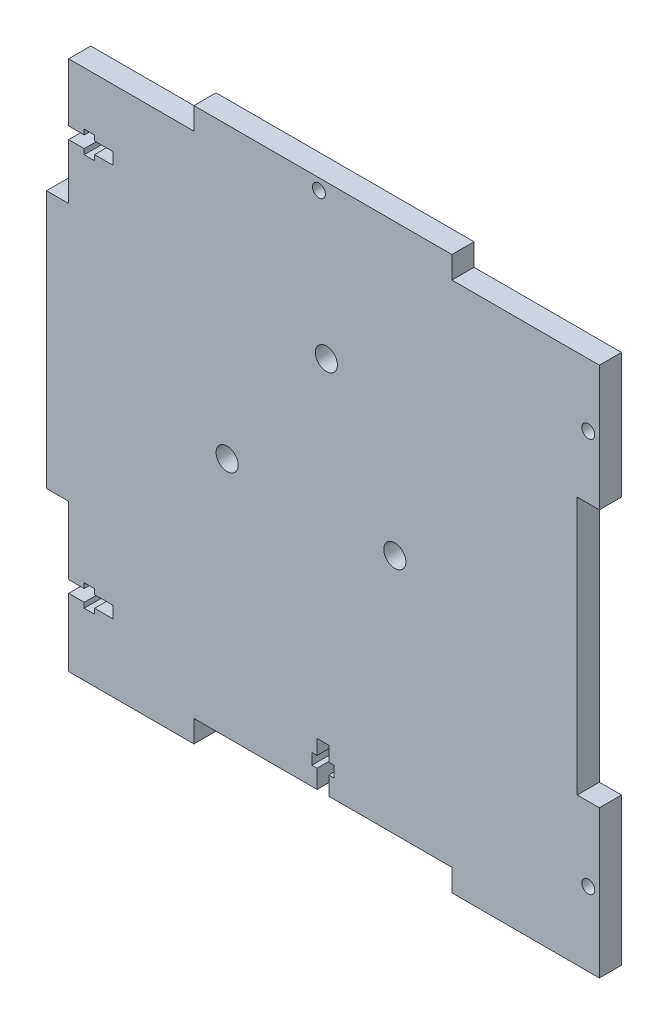
SolidWorks part; units mm, degrees
ref_plane "Front Plane" through (0, 0, 0) normal (0, 0, 1) x (1, 0, 0)
ref_plane "Top Plane" through (0, 0, 0) normal (0, 1, 0) x (1, 0, 0)
ref_plane "Right Plane" through (0, 0, 0) normal (1, 0, 0) x (0, 0, -1)
sketch "Sketch1" plane through (0, 0, 0) normal (0, 0, 1) x (1, 0, 0)
  line L0 (-38, 72) -> (-38, 78)
  line L1 (-72, -72) -> (72, -72)
  line L2 (-72, -72) -> (-72, 72)
  line L3 (-72, 72) -> (72, 72)
  line L4 (72, -72) -> (72, 72)
  line L5 (-72, -72) -> (72, 72) construction
  line L6 (-72, 72) -> (72, -72) construction
  line L7 (-38, 78) -> (32, 78)
  line L8 (32, 78) -> (32, 72)
  line L9 (-38, -72) -> (-38, -66)
  line L10 (-38, -66) -> (32, -66)
  line L11 (32, -66) -> (32, -72)
  line L12 (-72, 38) -> (-78, 38)
  line L13 (-78, 38) -> (-78, -32)
  line L14 (-78, -32) -> (-72, -32)
  line L15 (72, 38) -> (66, 38)
  line L16 (66, 38) -> (66, -32)
  line L17 (66, -32) -> (72, -32)
  line L18 (0, 108.2426) -> (0, -112.6743) construction
  line L19 (-72, 56.2) -> (-60, 56.2)
  line L24 (-72, -50.4) -> (-60, -50.4)
  line L25 (-72, -50.4) -> (-72, -53.6)
  line L26 (-72, -53.6) -> (-60, -53.6)
  line L27 (-60, -50.4) -> (-60, -53.6)
  line L28 (-67.7819, -49) -> (-64.967, -49)
  line L29 (-67.7819, -49) -> (-67.7819, -55)
  line L30 (-67.7819, -55) -> (-64.967, -55)
  line L31 (-64.967, -49) -> (-64.967, -55)
  line L32 (-72, 53) -> (-60, 53)
  line L33 (-60, 56.2) -> (-60, 53)
  line L34 (-67.7728, 57.6) -> (-64.958, 57.6)
  line L35 (-67.7728, 57.6) -> (-67.7728, 51.5685)
  line L36 (-67.7728, 51.5685) -> (-64.958, 51.5685)
  line L37 (-64.958, 57.6) -> (-64.958, 51.5685)
  line L39 (-4.6, -54) -> (-1.4, -54)
  line L40 (-4.6, -54) -> (-4.6, -66)
  line L41 (-4.6, -66) -> (-1.4, -66)
  line L42 (-1.4, -54) -> (-1.4, -66)
  line L43 (-6, -58) -> (0, -58)
  line L44 (-6, -58) -> (-6, -61)
  line L45 (-6, -61) -> (0, -61)
  line L46 (0, -58) -> (0, -61)
  circle A0 centre (69, 55) radius 1.75
  circle A3 centre (69, -52) radius 1.75
  circle A4 centre (-4.09, 75) radius 1.75
  point P0 (0, 0)
  dimension "D16" = 3.5
  dimension "D20" = 12
  dimension "D19" = 3.2
  dimension "D30" = 3
  dimension "D31" = 76.09
  dimension "D2" = 6
  dimension "D3" = 40
  dimension "D4" = 40
  dimension "D5" = 6
  dimension "D6" = 40
  dimension "D7" = 150
  dimension "D8" = 6
  dimension "D9" = 6
  dimension "D10" = 40
  dimension "D11" = 40
  dimension "D12" = 6
  dimension "D13" = 40
  dimension "D14" = 40
  dimension "D15" = 150
  dimension "D17" = 3
  dimension "D18" = 17
  dimension "D21" = 18.4
  dimension "D22" = 3
  dimension "D23" = 6
  dimension "D24" = 20
  dimension "D25" = 1.4
  dimension "D26" = 15
  dimension "D27" = 1.4
  dimension "D28" = 3.2
  dimension "D29" = 12
  dimension "D32" = 40
  dimension "D33" = 3.2
  dimension "D34" = 12
  dimension "D35" = 3
  dimension "D36" = 1.4
  dimension "D37" = 6
  dimension "D38" = 5
  dimension "D39" = 33.4
  dimension "D40" = 0
extrude "Boss-Extrude2" add sketch "Sketch1" along normal blind 6 contours L17 L16 L15 L4 L3 L2 L1 L9 L10 L11 | L13 L14 L2 L12 | L8 L7 L0 L3
sketch "Sketch2" plane through (0, 0, 0) normal (0, 0, -1) x (-1, 0, 0)
  circle A0 centre (2.0753, 36.4917) radius 3
  circle A1 centre (-16.5, -0.5) radius 3
  circle A2 centre (29, -0.5) radius 3
  point P6 (2.0753, 36.4917)
  point P8 (-16.5, -0.5)
  point P10 (29, -0.5)
extrude "Cut-Extrude1" cut sketch "Sketch2" against normal through all
equation "\"`2\"=15.927"
